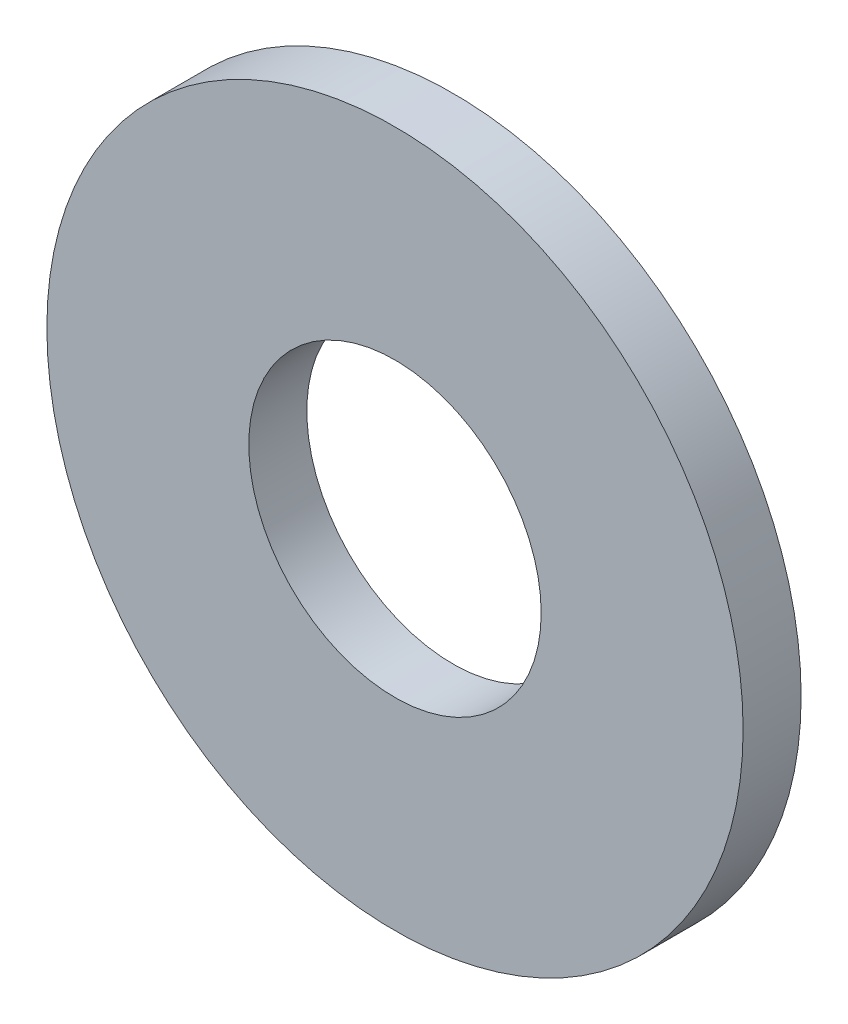
SolidWorks part; units mm, degrees
material "Aluminum Bronze"
ref_plane "Front Plane" through (0, 0, 0) normal (0, 0, 1) x (1, 0, 0)
ref_plane "Top Plane" through (0, 0, 0) normal (0, 1, 0) x (1, 0, 0)
ref_plane "Right Plane" through (0, 0, 0) normal (1, 0, 0) x (0, 0, -1)
sketch "Sketch1" plane through (0, 0, 0) normal (0, 0, 1) x (1, 0, 0)
  circle A0 centre (0, 0) radius 9.525
  circle A1 centre (0, 0) radius 4
  dimension "D1" = 19.05
  dimension "D2" = 8
extrude "Boss-Extrude1" add sketch "Sketch1" along normal blind 1.5875
